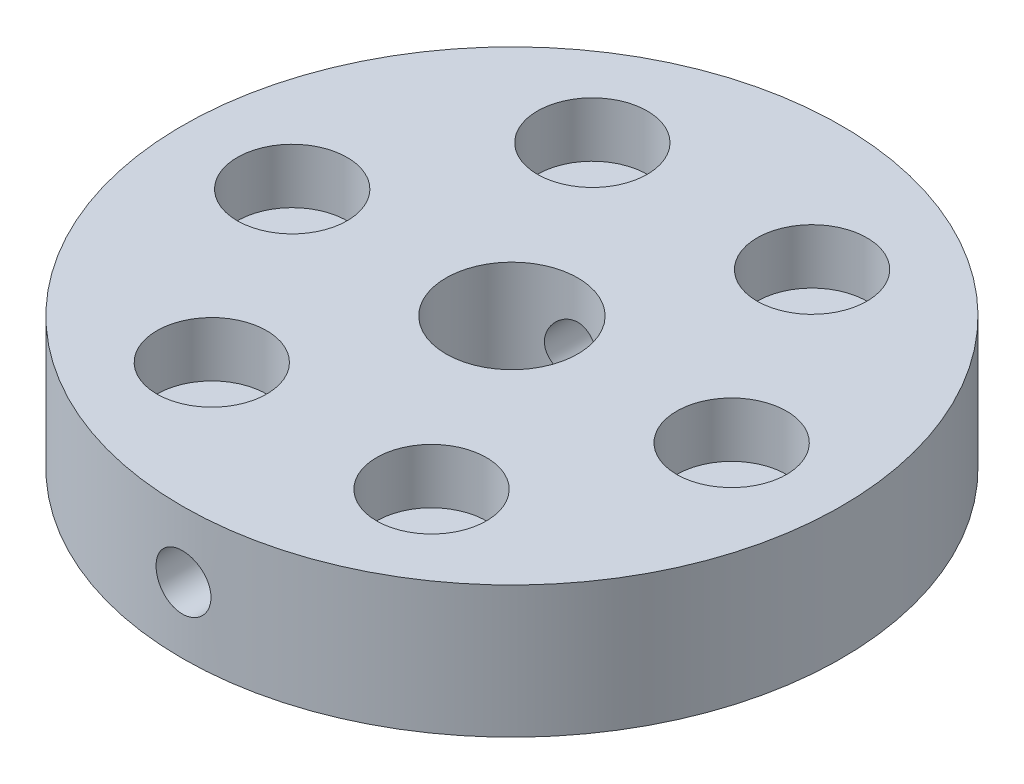
SolidWorks part; units mm, degrees
material "ABS"
ref_plane "Front Plane" through (0, 0, 0) normal (0, 0, 1) x (1, 0, 0)
ref_plane "Top Plane" through (0, 0, 0) normal (0, 1, 0) x (1, 0, 0)
ref_plane "Right Plane" through (0, 0, 0) normal (1, 0, 0) x (0, 0, -1)
sketch "Sketch1" plane through (0, 0, 0) normal (0, 1, 0) x (1, 0, 0)
  line L0 (0, 0) -> (108.2048, 0) construction
  circle A0 centre (0, 0) radius 30
  circle A1 centre (0, 0) radius 20 construction
  circle A2 centre (20, 0) radius 2
  circle A3 centre (10, -17.3205) radius 2
  circle A4 centre (-10, -17.3205) radius 2
  circle A5 centre (-20, 0) radius 2
  circle A6 centre (-10, 17.3205) radius 2
  circle A7 centre (10, 17.3205) radius 2
  circle A8 centre (0, 0) radius 6
  point P19 (0, 0)
  dimension "D1" = 60
  dimension "D2" = 40
  dimension "D3" = 4
  dimension "D5" = 12
  dimension "D4" = 6
extrude "Boss-Extrude1" add sketch "Sketch1" along normal blind 12
sketch "Sketch2" plane through (0, 0, 0) normal (0, 0, 1) x (1, 0, 0)
  line L0 (-30, 0) -> (30, 0) construction
  circle A0 centre (0, 6) radius 2.5
  dimension "D1" = 5
  dimension "D2" = 6
extrude "Cut-Extrude1" cut sketch "Sketch2" against normal through all and the other way through all
sketch "Sketch3" plane through (0, 12, 0) normal (0, 1, 0) x (1, 0, 0)
  circle A0 centre (0, 0) radius 20 construction
  circle A1 centre (-10, 17.3205) radius 5
  circle A2 centre (10, 17.3205) radius 5
  circle A3 centre (20, 0) radius 5
  circle A4 centre (10, -17.3205) radius 5
  circle A5 centre (-10, -17.3205) radius 5
  circle A6 centre (-20, 0) radius 5
  point P18 (0, 0)
  dimension "D1" = 40
  dimension "D2" = 10
  dimension "D3" = 6
extrude "Cut-Extrude2" cut sketch "Sketch3" against normal blind 5
